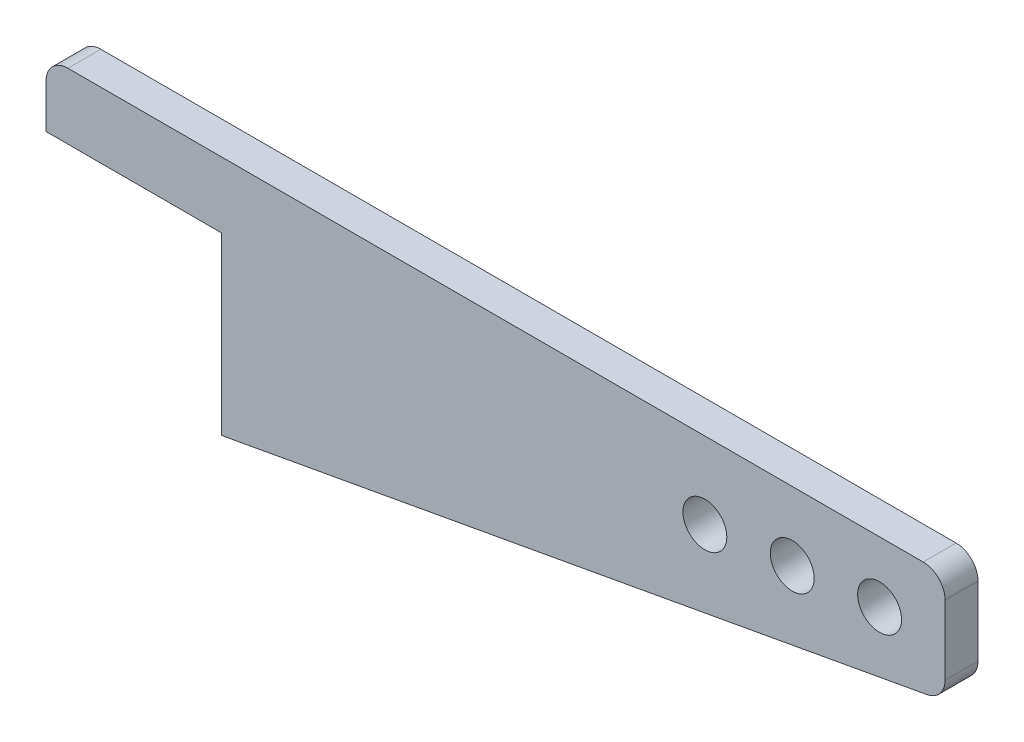
SolidWorks part; units mm, degrees
ref_plane "Plan de face" through (0, 0, 0) normal (0, 0, 1) x (1, 0, 0)
ref_plane "Plan de dessus" through (0, 0, 0) normal (0, 1, 0) x (1, 0, 0)
ref_plane "Plan de droite" through (0, 0, 0) normal (1, 0, 0) x (0, 0, -1)
sketch "Esquisse1" plane through (0, 0, 0) normal (0, 0, 1) x (1, 0, 0)
  line L0 (0, 0) -> (410, 0)
  line L1 (410, 0) -> (410, -50)
  line L2 (410, -50) -> (80, -110)
  line L3 (80, -110) -> (80, -30)
  line L4 (80, -30) -> (0, -30)
  line L5 (0, -30) -> (0, 0)
  line L6 (80, -110) -> (80, 0) construction
  line L7 (80, -55) -> (410, -25) construction
  circle A0 centre (300.4517, -34.9589) radius 10
  circle A1 centre (340.2875, -31.3375) radius 10
  circle A2 centre (380.1232, -27.7161) radius 10
  dimension "D6" = 20
  dimension "D1" = 410
  dimension "D2" = 50
  dimension "D3" = 110
  dimension "D4" = 80
  dimension "D5" = 80
  dimension "D7" = 40
  dimension "D8" = 40
  dimension "D9" = 30
extrude "Boss.-Extru.1" add sketch "Esquisse1" along normal blind 15
fillet "Congé1" radius 10 3 edges at (0, 0, 7.5) (410, -50, 7.5) (410, 0, 7.5)
